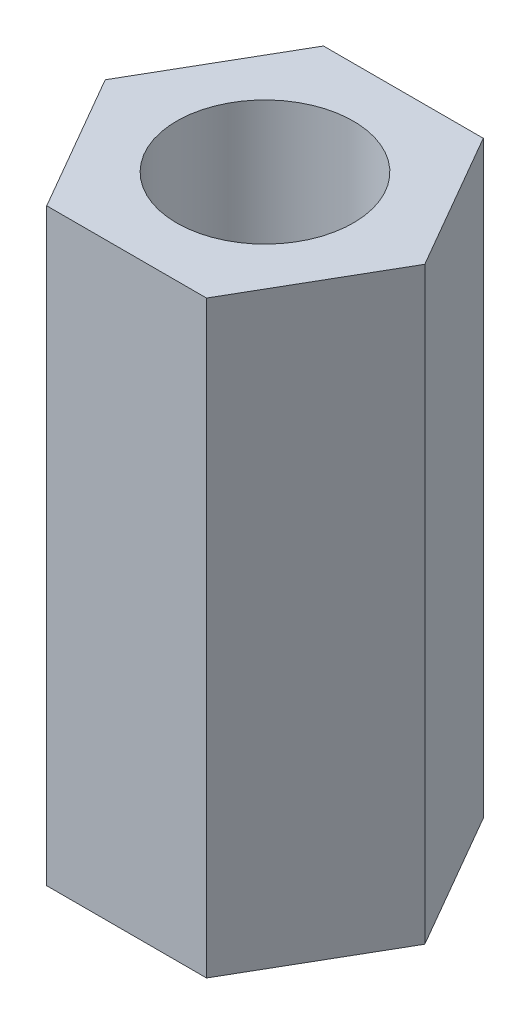
SolidWorks part; units mm, degrees
ref_plane "前视基准面" through (0, 0, 0) normal (0, 0, 1) x (1, 0, 0)
ref_plane "上视基准面" through (0, 0, 0) normal (0, 1, 0) x (1, 0, 0)
ref_plane "右视基准面" through (0, 0, 0) normal (1, 0, 0) x (0, 0, -1)
sketch "草图1" plane through (0, 0, 0) normal (0, 1, 0) x (1, 0, 0)
  line L1 (2.7135, 0) -> (1.3568, 2.35)
  line L2 (1.3568, 2.35) -> (-1.3568, 2.35)
  line L3 (-1.3568, 2.35) -> (-2.7135, 0)
  line L4 (-2.7135, 0) -> (-1.3568, -2.35)
  line L5 (-1.3568, -2.35) -> (1.3568, -2.35)
  line L6 (1.3568, -2.35) -> (2.7135, 0)
  circle A0 centre (0, 0) radius 2.35 construction
  dimension "D1" = 4.7
extrude "凸台-拉伸1" add sketch "草图1" along normal blind 10
sketch "草图2" plane through (0, 10, 0) normal (0, 1, 0) x (1, 0, 0)
  circle A0 centre (0, 0) radius 1.5
  dimension "D1" = 3
extrude "切除-拉伸1" cut sketch "草图2" against normal through all
